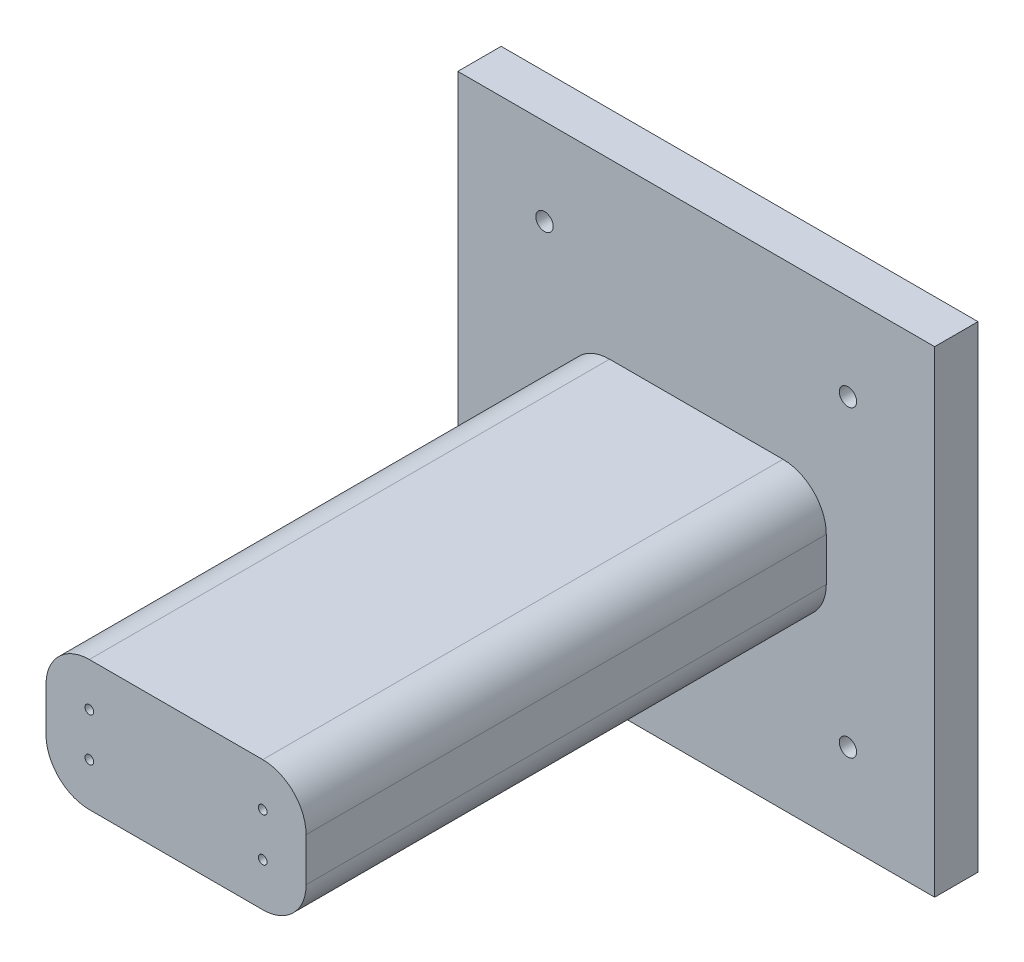
SolidWorks part; units mm, degrees
ref_plane "Plan de face" through (0, 0, 0) normal (0, 0, 1) x (1, 0, 0)
ref_plane "Plan de dessus" through (0, 0, 0) normal (0, 1, 0) x (1, 0, 0)
ref_plane "Plan de droite" through (0, 0, 0) normal (1, 0, 0) x (0, 0, -1)
sketch "Esquisse1" plane through (0, 0, 0) normal (0, 0, 1) x (1, 0, 0)
  line L1 (-27.5, 27.5) -> (27.5, 27.5)
  line L2 (-27.5, 27.5) -> (-27.5, -27.5)
  line L3 (-27.5, -27.5) -> (27.5, -27.5)
  line L4 (27.5, 27.5) -> (27.5, -27.5)
  line L5 (-27.5, 27.5) -> (27.5, -27.5) construction
  line L6 (-27.5, -27.5) -> (27.5, 27.5) construction
  point P0 (0, 0)
  dimension "D1" = 55
  dimension "D2" = 55
extrude "Boss.-Extru.1" add sketch "Esquisse1" along normal blind 5
sketch "Esquisse2" plane through (0, 0, 5) normal (0, 0, 1) x (1, 0, 0)
  line L1 (-15, 7.5) -> (15, 7.5)
  line L2 (-15, 7.5) -> (-15, -7.5)
  line L3 (-15, -7.5) -> (15, -7.5)
  line L4 (15, 7.5) -> (15, -7.5)
  line L5 (-15, 7.5) -> (15, -7.5) construction
  line L6 (-15, -7.5) -> (15, 7.5) construction
  point P0 (0, 0)
  dimension "D1" = 15
  dimension "D2" = 30
extrude "Boss.-Extru.2" add sketch "Esquisse2" along normal blind 60
fillet "Congé2" radius 5 1 edges at (-15, -7.5, 35)
fillet "Congé3" radius 5 1 edges at (15, 7.5, 35)
fillet "Congé4" radius 5 1 edges at (15, -7.5, 35)
fillet "Congé5" radius 5 1 edges at (-15, 7.5, 35)
sketch "Esquisse3" plane through (0, 0, 5) normal (0, 0, 1) x (1, 0, 0)
  line L0 (17.5, 27.5) -> (17.5, -37.2325) construction
  line L1 (27.5, 27.5) -> (-27.5, 27.5) construction
  line L2 (-17.5, 27.5) -> (-17.5, -34.8708) construction
  line L3 (27.5, -27.5) -> (27.5, 27.5) construction
  line L4 (27.5, 17.5) -> (-29.5387, 17.5) construction
  line L5 (27.5, -17.5) -> (-28.3793, -17.5) construction
  line L6 (-27.5, -27.5) -> (27.5, -27.5) construction
  line L7 (-27.5, 27.5) -> (-27.5, -27.5) construction
  circle A0 centre (17.5, 17.5) radius 1
  circle A1 centre (-17.5, 17.5) radius 1
  circle A2 centre (-17.5, -17.5) radius 1
  circle A3 centre (17.5, -17.5) radius 1
  dimension "D3" = 2
  dimension "D6" = 2
  dimension "D7" = 2
  dimension "D8" = 2
  dimension "D1" = 10
  dimension "D2" = 10
  dimension "D4" = 10
  dimension "D5" = 10
extrude "Enlèv. mat.-Extru.1" cut sketch "Esquisse3" against normal up to next
sketch "Esquisse4" plane through (0, 0, 65) normal (0, 0, 1) x (1, 0, 0)
  line L0 (10, -7.5) -> (10, 7.5) construction
  line L1 (-10, -7.5) -> (10, -7.5) construction
  line L2 (10, 7.5) -> (-10, 7.5) construction
  line L3 (-10, -7.5) -> (-10, 7.5) construction
  line L4 (-15, -2.5) -> (15, -2.5) construction
  line L5 (15, 2.5) -> (-15, 2.5) construction
  line L6 (15, -2.5) -> (15, 2.5) construction
  line L7 (-15, 2.5) -> (-15, -2.5) construction
  circle A0 centre (10, -2.5) radius 0.5
  circle A1 centre (10, 2.5) radius 0.5
  circle A2 centre (-10, 2.5) radius 0.5
  circle A3 centre (-10, -2.5) radius 0.5
  dimension "D5" = 1
  dimension "D6" = 1
  dimension "D7" = 1
  dimension "D8" = 1
  dimension "D1" = 5
  dimension "D2" = 5
  dimension "D3" = 5
  dimension "D4" = 5
extrude "Enlèv. mat.-Extru.2" cut sketch "Esquisse4" against normal blind 2
